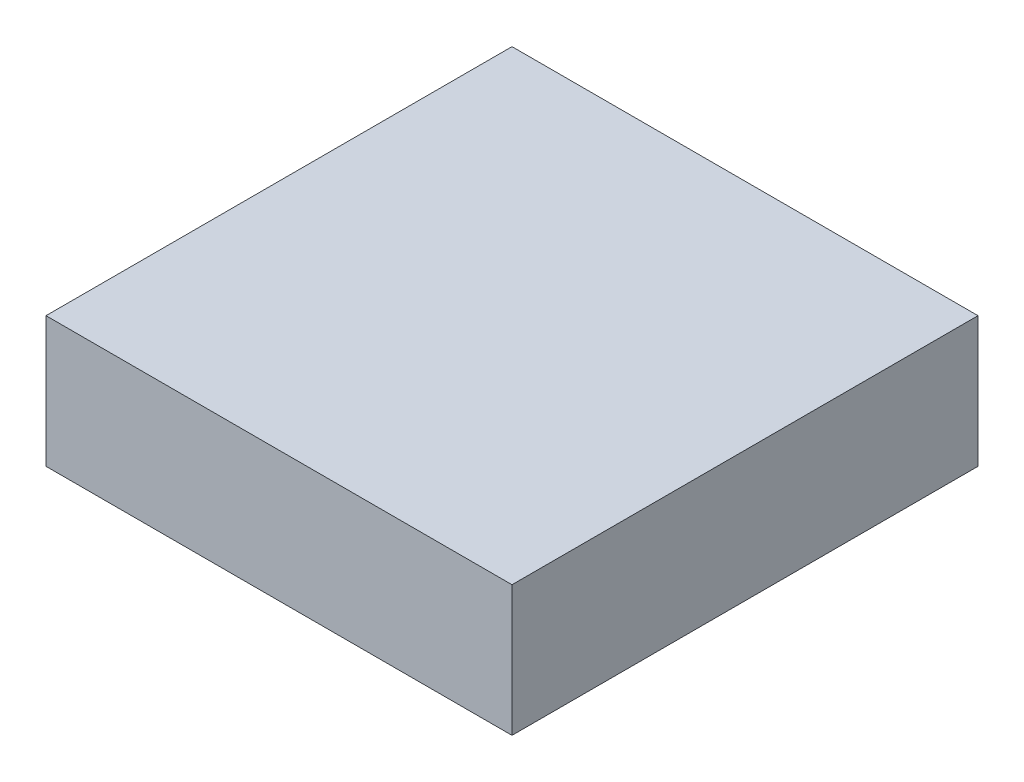
SolidWorks part; units mm, degrees
material "1060 Alloy"
ref_plane "Front Plane" through (0, 0, 0) normal (0, 0, 1) x (1, 0, 0)
ref_plane "Top Plane" through (0, 0, 0) normal (0, 1, 0) x (1, 0, 0)
ref_plane "Right Plane" through (0, 0, 0) normal (1, 0, 0) x (0, 0, -1)
sketch "Sketch1" plane through (0, 0, 0) normal (0, 1, 0) x (1, 0, 0)
  line L0 (-22.5, 22.5) -> (22.5, -22.5) construction
  line L1 (-22.5, 22.5) -> (22.5, 22.5)
  line L2 (-22.5, 22.5) -> (-22.5, -22.5)
  line L3 (-22.5, -22.5) -> (22.5, -22.5)
  line L4 (22.5, 22.5) -> (22.5, -22.5)
  dimension "D1" = 45
extrude "Boss-Extrude1" add sketch "Sketch1" along normal blind 12.6
